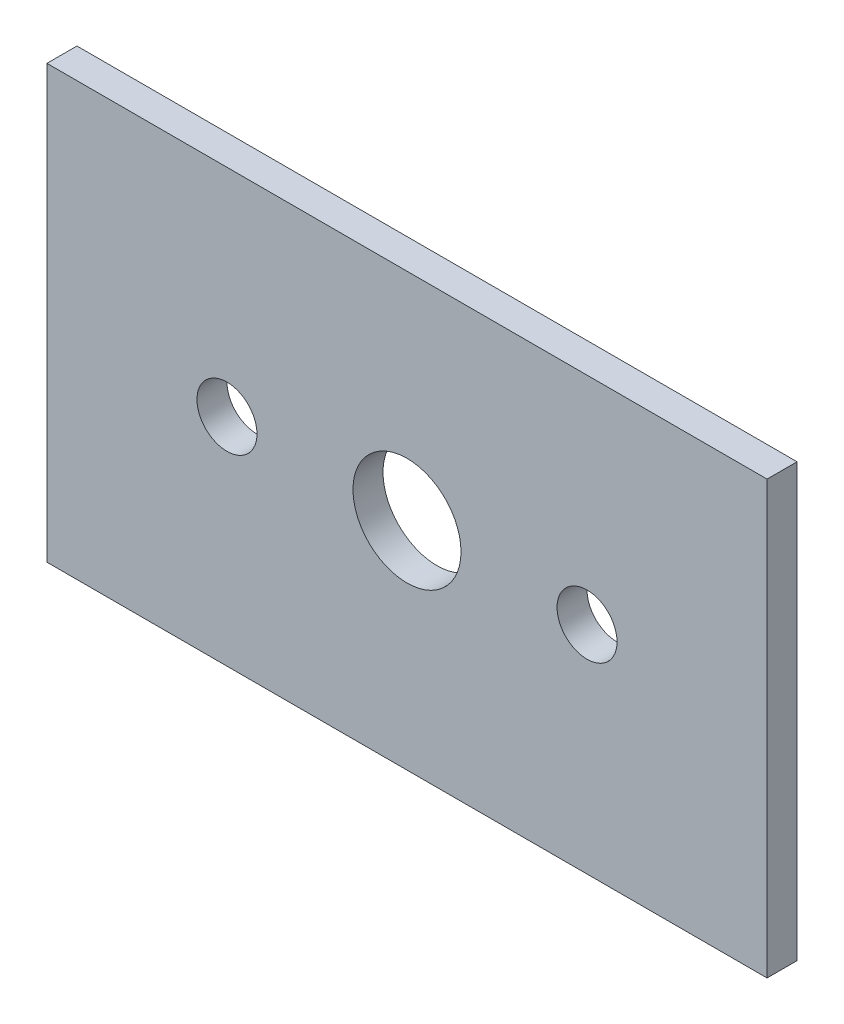
SolidWorks part; units mm, degrees
ref_plane "Front Plane" through (0, 0, 0) normal (0, 0, 1) x (1, 0, 0)
ref_plane "Top Plane" through (0, 0, 0) normal (0, 1, 0) x (1, 0, 0)
ref_plane "Right Plane" through (0, 0, 0) normal (1, 0, 0) x (0, 0, -1)
sketch "Sketch1" plane through (0, 0, 0) normal (0, 0, 1) x (1, 0, 0)
  line L1 (0, 0) -> (152.4, 0)
  line L2 (0, 0) -> (0, 91.44)
  line L3 (0, 91.44) -> (152.4, 91.44)
  line L4 (152.4, 0) -> (152.4, 91.44)
  dimension "D1" = 91.44
  dimension "D2" = 152.4
extrude "Boss-Extrude1" add sketch "Sketch1" along normal blind 6.35 contours L3 L4 L1 L2
sketch "Sketch2" plane through (0, 0, 6.35) normal (0, 0, 1) x (1, 0, 0)
  line L0 (0, 0) -> (0, 91.44) construction
  line L1 (0, 0) -> (152.4, 0) construction
  circle A0 centre (76.2, 45.72) radius 11.43
  circle A1 centre (114.3, 45.72) radius 6.35
  circle A2 centre (38.1, 45.72) radius 6.35
  dimension "D1" = 12.7
  dimension "D2" = 12.7
  dimension "D3" = 22.86
  dimension "D4" = 76.2
  dimension "D5" = 38.1
  dimension "D6" = 38.1
  dimension "D7" = 45.72
  dimension "D8" = 45.72
  dimension "D9" = 45.72
extrude "Cut-Extrude1" cut sketch "Sketch2" against normal blind 6.35
